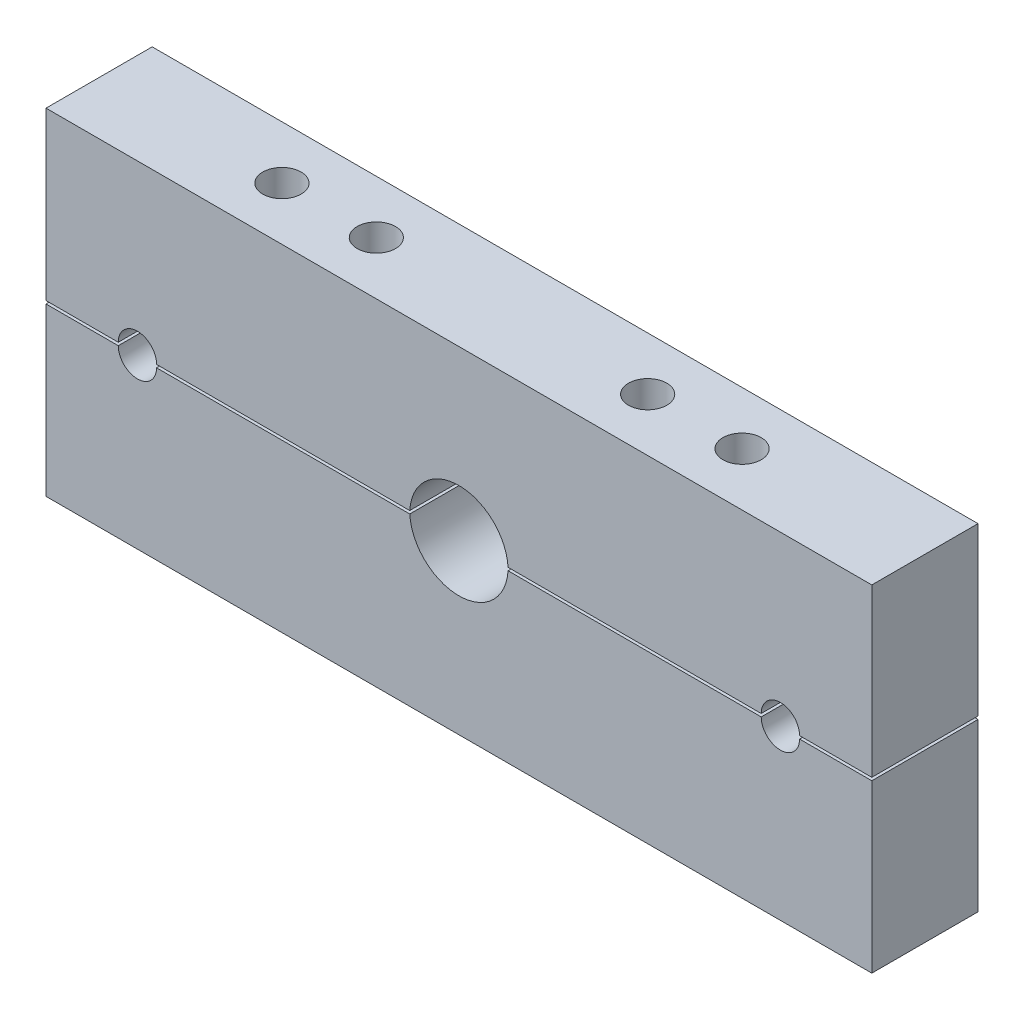
SolidWorks part; units mm, degrees
ref_plane "Plano frontal" through (0, 0, 0) normal (0, 0, 1) x (1, 0, 0)
ref_plane "Plano superior" through (0, 0, 0) normal (0, 1, 0) x (1, 0, 0)
ref_plane "Plano direito" through (0, 0, 0) normal (1, 0, 0) x (0, 0, -1)
sketch "Sketch1" plane through (0, 0, 0) normal (0, 0, 1) x (1, 0, 0)
  line L0 (81.8295, -84.5197) -> (81.8295, -142.0197) construction
  line L1 (-12.1705, -84.5197) -> (267.8295, -84.5197)
  line L2 (-12.1705, -84.5197) -> (-12.1705, -142.0197)
  line L3 (-12.1705, -142.0197) -> (267.8295, -142.0197)
  line L4 (267.8295, -84.5197) -> (267.8295, -142.0197)
  line L5 (49.8295, -84.5197) -> (49.8295, -142.0197) construction
  line L6 (18.8295, -142.0197) -> (18.8295, -84.5197) construction
  line L7 (236.8295, -84.5197) -> (236.8295, -142.0197) construction
  circle A0 centre (127.8295, -142.0197) radius 16.7
  circle A1 centre (18.8295, -142.0197) radius 6.5
  circle A2 centre (236.8295, -142.0197) radius 6.5
  dimension "D1" = 33.4
  dimension "D6" = 13
  dimension "D2" = 57.5
  dimension "D3" = 32
  dimension "D4" = 62
  dimension "D5" = 280
  dimension "D7" = 31
  dimension "D8" = 31
extrude "Boss-Extrude1" add sketch "Sketch1" along normal blind 36 contours A2 L3 L4 L1 L2 A1 A0 | L3 A2 | L3 A1
sketch "Sketch2" plane through (-12.1705, 0, 0) normal (-1, 0, 0) x (0, 0, 1)
  line L0 (36, -84.5197) -> (36, -142.0197) construction
  line L1 (0, -142.0197) -> (36, -142.0197)
  line L2 (0, -142.0197) -> (0, -141.5197)
  line L3 (0, -141.5197) -> (36, -141.5197)
  line L4 (36, -142.0197) -> (36, -141.5197)
  dimension "D1" = 0.5
extrude "Cut-Extrude1" cut sketch "Sketch2" against normal through all
sketch "Sketch4" plane through (0, -84.5197, 0) normal (0, 1, 0) x (1, 0, 0)
  line L0 (49.8295, 0) -> (49.8295, -36) construction
  line L1 (-12.1705, -36) -> (267.8295, -36) construction
  line L2 (81.8295, 0) -> (81.8295, -36) construction
  line L3 (-12.1705, -18) -> (49.8295, -18) construction
  line L4 (-12.1705, -36) -> (-12.1705, 0) construction
  line L5 (49.8295, -18) -> (81.8295, -18) construction
  line L6 (267.8295, -18) -> (205.8295, -18) construction
  line L7 (267.8295, -36) -> (267.8295, 0) construction
  line L8 (205.8295, -18) -> (173.8295, -18) construction
  circle A0 centre (205.8295, -18) radius 6.5
  circle A1 centre (173.8295, -18) radius 6.5
  circle A2 centre (81.8295, -18) radius 6.5
  circle A3 centre (49.8295, -18) radius 6.5
  dimension "D1" = 13
extrude "Cut-Extrude3" cut sketch "Sketch4" against normal through all
mirror "Mirror1" about plane through (267.8295, -141.5197, 0) normal (0, 1, 0) of "Cut-Extrude3", "Boss-Extrude1", "Cut-Extrude1"
sketch "Sketch5" plane through (-12.1705, 0, 0) normal (-1, 0, 0) x (0, 0, 1)
  line L0 (36, -141.5197) -> (36, -198.5197) construction
  line L1 (0, -141.5197) -> (36, -141.5197)
  line L2 (0, -141.5197) -> (0, -142.0197)
  line L3 (0, -142.0197) -> (36, -142.0197)
  line L4 (36, -141.5197) -> (36, -142.0197)
  line L5 (0, -84.5197) -> (0, -141.0197) construction
  line L6 (36, -84.5197) -> (36, -141.0197) construction
  point P4 (0, 0)
  point P7 (0, 0)
  point P8 (0, -142.8727)
  point P11 (36, -152.1924)
  point P15 (0, 0)
  point P16 (36, -141.7024)
  point P17 (0, 0)
  dimension "D1" = 0.5
extrude "Cut-Extrude4" cut sketch "Sketch5" against normal through all
sketch "Sketch3" plane through (0, 0, 36) normal (0, 0, 1) x (1, 0, 0)
  line L2 (18.8295, -142.0197) -> (18.8295, -84.5197) construction
  line L3 (236.8295, -84.5197) -> (236.8295, -142.0197) construction
  line L4 (12.3295, -141.0197) -> (243.3295, -141.0197) construction
  line L5 (111.1595, -141.0197) -> (-12.1705, -141.0197) construction
  line L6 (111.1595, -142.0197) -> (-12.1705, -142.0197) construction
  line L8 (267.8295, -142.0197) -> (144.4995, -142.0197) construction
  line L9 (12.3295, -142.0197) -> (243.3295, -142.0197) construction
  line L10 (12.3295, -141.0197) -> (25.3295, -141.0197)
  line L11 (12.3295, -142.0197) -> (25.3295, -142.0197)
  line L12 (230.3295, -142.0197) -> (243.3295, -142.0197)
  line L13 (230.3295, -141.0197) -> (243.3295, -141.0197)
  arc A0 (25.3295, -141.0197) -> (12.3295, -141.0197) centre (18.8295, -141.0197) ccw
  arc A1 (243.3295, -141.0197) -> (230.3295, -141.0197) centre (236.8295, -141.0197) ccw
  arc A2 (12.3295, -142.0197) -> (25.3295, -142.0197) centre (18.8295, -142.0197) ccw
  arc A3 (230.3295, -142.0197) -> (243.3295, -142.0197) centre (236.8295, -142.0197) ccw
  line M11 (-12.1705, -141.0197) -> (111.1595, -141.0197)
  line M12 (144.4995, -141.0197) -> (267.8295, -141.0197)
  dimension "D1" = 13
extrude "Cut-Extrude5" cut sketch "Sketch3" against normal through all contours A0 M11 | A1 M12 | L11 A2 | L12 A3
